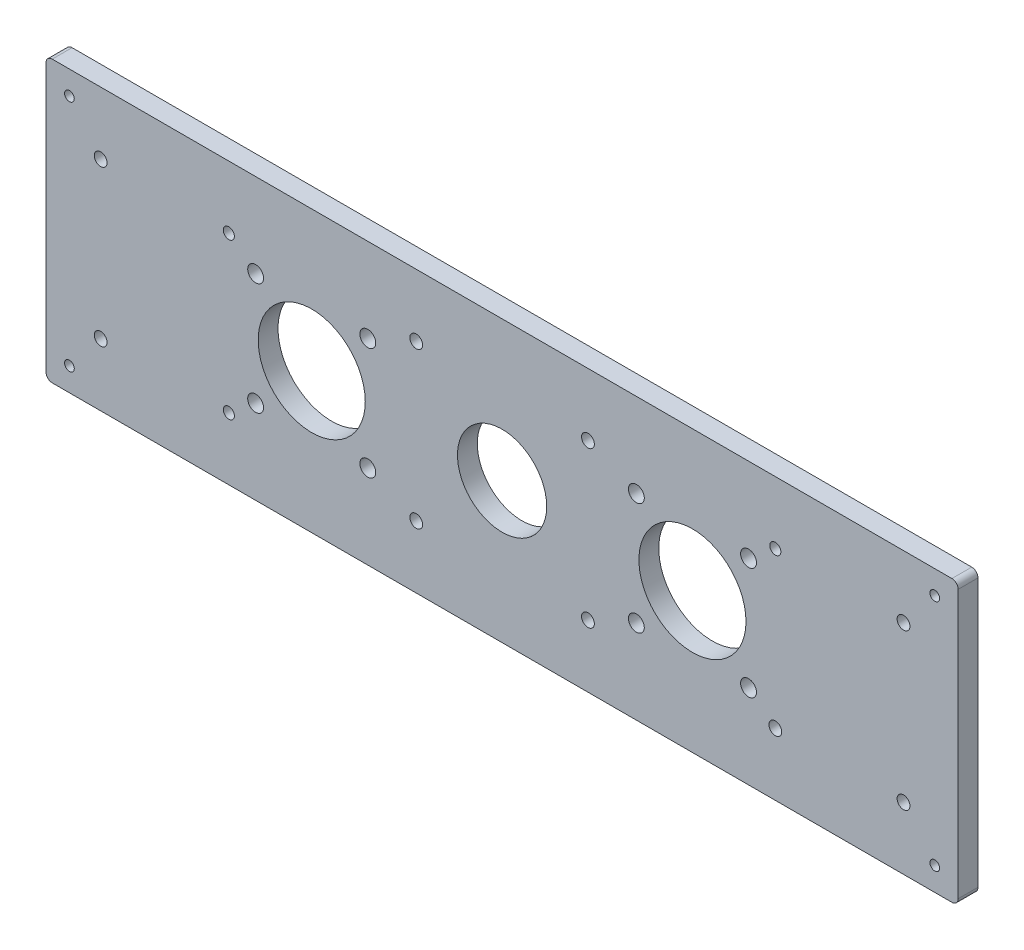
SolidWorks part; units mm, degrees
ref_plane "Front Plane" through (0, 0, 0) normal (0, 0, 1) x (1, 0, 0)
ref_plane "Top Plane" through (0, 0, 0) normal (0, 1, 0) x (1, 0, 0)
ref_plane "Right Plane" through (0, 0, 0) normal (1, 0, 0) x (0, 0, -1)
sketch "Sketch1" plane through (0, 0, 0) normal (0, 0, 1) x (1, 0, 0)
  line L1 (0, 0) -> (292.1, 0)
  line L2 (0, 0) -> (0, 89.8)
  line L3 (0, 89.8) -> (292.1, 89.8)
  line L4 (292.1, 0) -> (292.1, 89.8)
  circle A3 centre (146.05, 44.9) radius 14.2875
  point P7 (146.05, 44.9)
  circle B0 centre (103.0516, 62.8594) radius 2.54
  circle B1 centre (103.0494, 26.9384) radius 2.54
  circle B2 centre (67.1284, 26.9406) radius 2.54
  circle B3 centre (67.1306, 62.8616) radius 2.54
  circle B4 centre (85.09, 44.9) radius 17.145
  circle B5 centre (189.0506, 62.8616) radius 2.54
  circle B6 centre (224.9716, 62.8594) radius 2.54
  circle B7 centre (224.9694, 26.9384) radius 2.54
  circle B8 centre (189.0484, 26.9406) radius 2.54
  circle B9 centre (207.01, 44.9) radius 17.145
  dimension "D3" = 60.96
  dimension "D4" = 60.96
  dimension "D5" = 146.05
  dimension "D6" = 28.575
  dimension "D1" = 89.8
  dimension "D2" = 292.1
sketch_block_instance "Block1-1"
sketch_block "Block1" parameters "D1"=5.08, "D2"=34.29
sketch_block_instance "Block2-1"
sketch_block "Block2" parameters "D1"=5.08, "D2"=34.29
extrude "Boss-Extrude1" add sketch "Sketch1" along normal blind 6.35
sketch "Sketch2" plane through (0, 0, 6.35) normal (0, 0, 1) x (1, 0, 0)
  line L0 (292.1, 89.8) -> (0, 89.8) construction
  line L1 (108.55, 0) -> (183.55, 0)
  line L2 (108.55, 0) -> (108.55, 89.8)
  line L3 (108.55, 89.8) -> (183.55, 89.8)
  line L4 (183.55, 0) -> (183.55, 89.8)
  line L5 (108.55, 0) -> (183.55, 89.8) construction
  line L6 (108.55, 89.8) -> (183.55, 0) construction
  line L7 (108.55, 44.9) -> (146.05, 44.9) construction
  line L8 (108.55, 89.8) -> (-29.3949, 89.8)
  line L9 (108.55, 89.8) -> (108.55, -10.172)
  line L10 (108.55, -10.172) -> (-29.3949, -10.172)
  line L11 (-29.3949, 89.8) -> (-29.3949, -10.172)
  line L12 (183.55, 89.8) -> (343.3103, 89.8)
  line L13 (183.55, 89.8) -> (183.55, -29.3261)
  line L14 (183.55, -29.3261) -> (343.3103, -29.3261)
  line L15 (343.3103, 89.8) -> (343.3103, -29.3261)
  line L16 (146.05, 44.9) -> (146.05, 89.8) construction
  circle A0 centre (118.55, 20) radius 2.05
  circle A1 centre (118.55, 69.8) radius 2.05
  circle A2 centre (173.55, 20) radius 2.05
  circle A3 centre (173.55, 69.8) radius 2.05
  point P0 (146.05, 44.9)
  dimension "D2" = 4.1
  dimension "D3" = 20
  dimension "D1" = 75
  dimension "D4" = 10
extrude "Cut-Extrude1" cut sketch "Sketch2" against normal blind 10 contours A0 | A1 | A3 | A2
sketch "Sketch3" plane through (0, 0, 6.35) normal (0, 0, 1) x (1, 0, 0)
  line L0 (0, 0) -> (292.1, 0) construction
  line L1 (292.1, 0) -> (292.1, 89.8) construction
  line L2 (146.05, 0) -> (146.05, 11.9893) construction
  line L3 (292.1, 44.9) -> (277.1, 44.9) construction
  circle A0 centre (284.6, 7.5) radius 1.55
  circle A1 centre (7.5, 7.5) radius 1.55
  circle A2 centre (7.5, 82.3) radius 1.55
  circle A3 centre (284.6, 82.3) radius 1.55
  circle A4 centre (274.6, 20) radius 2.05
  circle A5 centre (17.5, 20) radius 2.05
  circle A6 centre (17.5, 69.8) radius 2.05
  circle A7 centre (274.6, 69.8) radius 2.05
  circle A8 centre (173.55, 20) radius 2.05 construction
  dimension "D1" = 3.1
  dimension "D4" = 4.1
  dimension "D2" = 7.5
  dimension "D3" = 7.5
  dimension "D5" = 10
  dimension "D6" = 0
extrude "Cut-Extrude2" cut sketch "Sketch3" against normal blind 10 contours A4 | A0 | A7 | A3 | A6 | A2 | A1 | A5
fillet "Fillet1" radius 2 4 edges at (0, 0, 3.175) (0, 89.8, 3.175) (292.1, 89.8, 3.175) (292.1, 0, 3.175)
sketch "Sketch4" plane through (0, 0, 6.35) normal (0, 0, 1) x (1, 0, 0)
  line L1 (233.55, 69.8) -> (58.55, 69.8)
  line L2 (233.55, 69.8) -> (233.55, 20)
  line L3 (233.55, 20) -> (58.55, 20)
  line L4 (58.55, 69.8) -> (58.55, 20)
  line L5 (233.55, 69.8) -> (58.55, 20) construction
  line L6 (233.55, 20) -> (58.55, 69.8) construction
  circle A0 centre (233.55, 20) radius 2.05
  circle A1 centre (233.55, 69.8) radius 1.778
  circle A2 centre (58.55, 69.8) radius 1.778
  circle A3 centre (58.55, 20) radius 1.778
  point P0 (146.05, 44.9)
  dimension "D2" = 4.1
  dimension "D3" = 3.556
  dimension "D4" = 3.556
  dimension "D5" = 3.556
  dimension "D1" = 175
extrude "Cut-Extrude4" cut sketch "Sketch4" against normal through all contours A0 | A1 | A2 | A3
